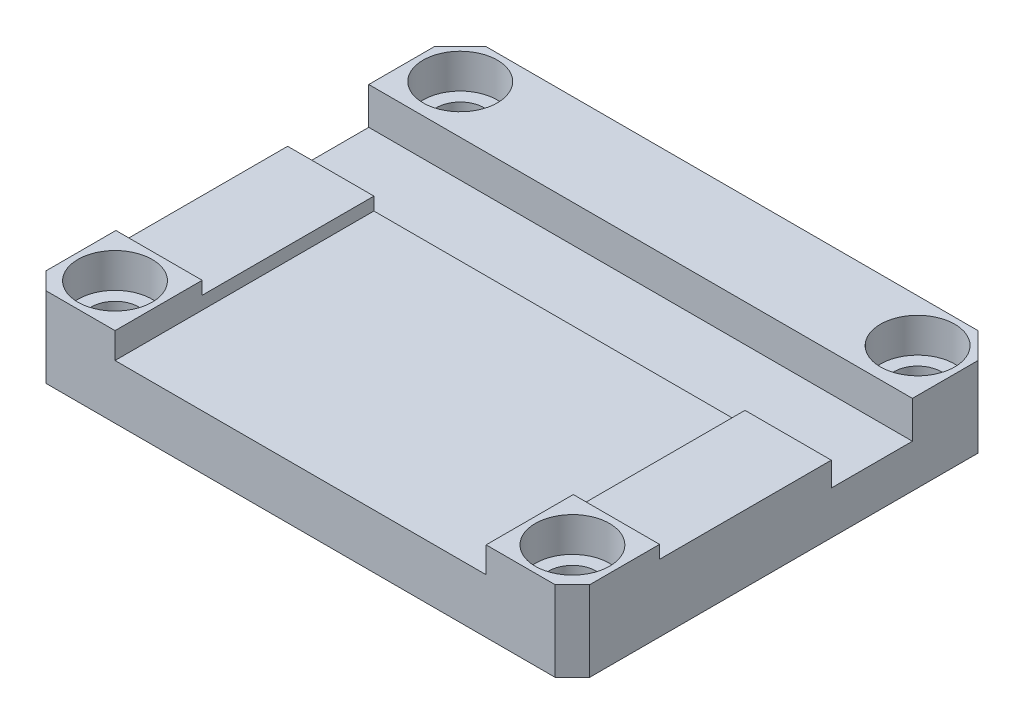
SolidWorks part; units mm, degrees
ref_plane "Front Plane" through (0, 0, 0) normal (0, 0, 1) x (1, 0, 0)
ref_plane "Top Plane" through (0, 0, 0) normal (0, 1, 0) x (1, 0, 0)
ref_plane "Right Plane" through (0, 0, 0) normal (1, 0, 0) x (0, 0, -1)
sketch "Sketch1" plane through (0, 0, 0) normal (0, 1, 0) x (1, 0, 0)
  line L1 (-31.5, -25) -> (31.5, -25)
  line L2 (-31.5, -25) -> (-31.5, 25)
  line L3 (-31.5, 25) -> (31.5, 25)
  line L4 (31.5, -25) -> (31.5, 25)
  line L5 (-31.5, -25) -> (31.5, 25) construction
  line L6 (-31.5, 25) -> (31.5, -25) construction
  point P0 (0, 0)
  dimension "D1" = 63
  dimension "D2" = 50
extrude "Boss-Extrude1" add sketch "Sketch1" along normal blind 9.3
sketch "Sketch2" plane through (0, 9.3, 0) normal (0, 1, 0) x (1, 0, 0)
  line L0 (0, 0) -> (0, 25) construction
  line L1 (31.5, 25) -> (-31.5, 25) construction
  line L2 (-26.5, 20) -> (-26.5, -20) construction
  line L4 (-31.5, 25) -> (-31.5, -25) construction
  circle A0 centre (-26.5, -20) radius 3.3086
  circle A1 centre (-26.5, 20) radius 3.3086
  circle A2 centre (26.5, -20) radius 3.3086
  circle A3 centre (26.5, 20) radius 3.3086
  point P9 (26.5, -20)
  point P10 (26.5, 20)
  dimension "D1" = 5
  dimension "D2" = 5
  dimension "D3" = 40
hole_wizard "CBORE for M5 Hex Socket Head Cap Screw2" positions "3DSketch2" profile "Sketch4" counterbore size "M5" standard "ISO" end condition through all
sketch3d "3DSketch2"
  point P0 (-26.5, 9.3, 20)
  point P3 (26.5, 9.3, 20)
  point P6 (26.5, 9.3, -20)
  point P9 (-26.5, 9.3, -20)
sketch "Sketch4" plane through (-26.5, 9.3, 20) normal (1, 0, 0) x (0, 0, 1)
  line L0 (0, 0) -> (0, 9.3)
  line L1 (0, 9.3) -> (2.75, 9.3)
  line L3 (2.75, 9.3) -> (2.75, 4)
  line L4 (2.75, 4) -> (4.3, 4)
  line L5 (4.3, 4) -> (4.3, 0)
  line L7 (4.3, 0) -> (0, 0)
  line L11 (0, -6.35) -> (0, 107.95) construction
  dimension "Thru Hole Dia." = 5.5
  dimension "Thru Hole Depth" = 9.3
  dimension "C'Bore Dia." = 8.6
  dimension "C'Bore Depth" = 4
chamfer "Chamfer1" distance 3 angle 45 2 edges at (31.5, 4.65, -25) (-31.5, 4.65, -25)
chamfer "Chamfer2" distance 2 angle 45 2 edges at (-31.5, 4.65, 25) (31.5, 4.65, 25)
sketch "Sketch5" plane through (0, 9.3, 0) normal (0, 1, 0) x (1, 0, 0)
  line L0 (0, 0) -> (0, 25) construction
  line L1 (28.5, 25) -> (-28.5, 25) construction
  line L2 (0, -25) -> (-21.5, -25)
  line L3 (-29.5, -25) -> (29.5, -25) construction
  line L4 (-21.5, -25) -> (-21.5, 14.4)
  line L5 (-21.5, 14.4) -> (21.5, 14.4)
  line L6 (21.5, 14.4) -> (21.5, -25)
  line L7 (21.5, -25) -> (0, -25)
  line L8 (-21.5, 5) -> (21.5, 5) construction
  dimension "D1" = 30
  dimension "D2" = 9.4
  dimension "D3" = 21.5
  dimension "D4" = 21.5
extrude "Cut-Extrude1" cut sketch "Sketch5" against normal blind 3
sketch "Sketch7" plane through (0, 9.3, 0) normal (0, 1, 0) x (1, 0, 0)
  line L0 (-21.5, 14.4) -> (31.5, 14.4)
  line L1 (31.5, -23) -> (31.5, 22) construction
  line L2 (31.5, 14.4) -> (31.5, 5)
  line L3 (31.5, 5) -> (-31.5, 5)
  line L4 (-31.5, 22) -> (-31.5, -23) construction
  line L5 (-31.5, 5) -> (-31.5, 14.4)
  line L6 (-31.5, 14.4) -> (-21.5, 14.4)
  dimension "D1" = 9.4
extrude "Cut-Extrude2" cut sketch "Sketch7" against normal offset from surface (4.3 mm away) 4.3 up to face at (-26.5, 9.3, 24.3)
sketch "Sketch8" plane through (0, 9.3, 0) normal (0, 1, 0) x (1, 0, 0)
  line L0 (31.5, 5) -> (21.5, 5)
  line L1 (21.5, 5) -> (21.5, -14.9)
  line L2 (21.5, -25) -> (21.5, 5) construction
  line L3 (21.5, -14.9) -> (31.5, -14.9)
  line L4 (31.5, -23) -> (31.5, 5) construction
  line L5 (31.5, -14.9) -> (31.5, 5)
  line L6 (-31.5, 5) -> (-21.5, 5)
  line L7 (-21.5, 5) -> (-21.5, -14.9)
  line L8 (-21.5, 5) -> (-21.5, -25) construction
  line L9 (-21.5, -14.9) -> (-31.5, -14.9)
  line L10 (-31.5, 5) -> (-31.5, -23) construction
  line L11 (-31.5, -14.9) -> (-31.5, 5)
  dimension "D1" = 19.9
  dimension "D2" = 19.9
extrude "Cut-Extrude3" cut sketch "Sketch8" against normal blind 1.5
